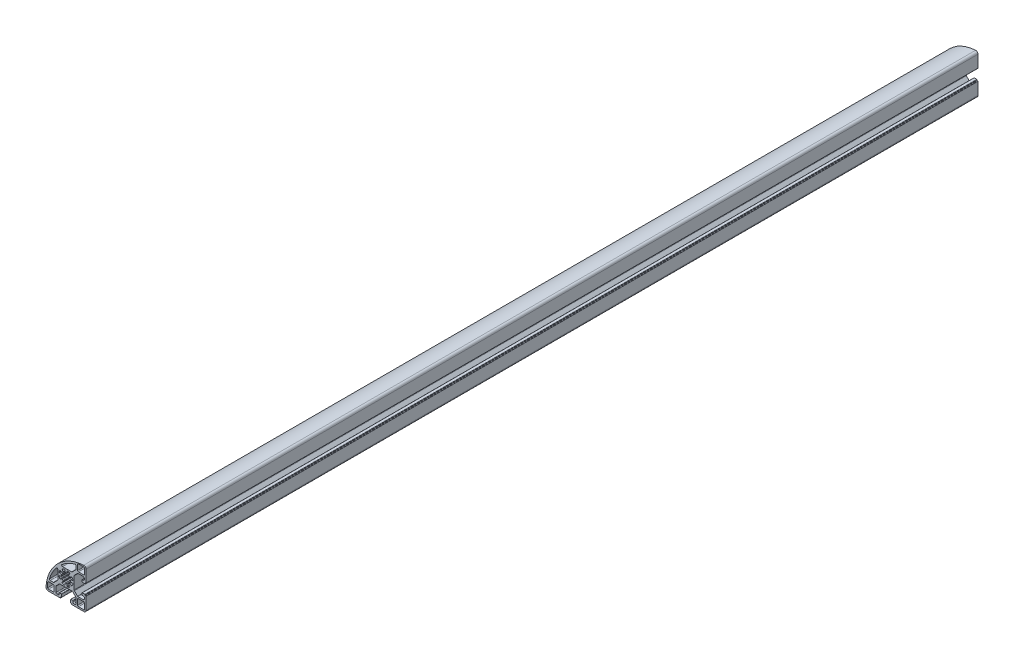
SolidWorks part; units mm, degrees
material "6063 T5"
ref_plane "Спереди" through (0, 0, 0) normal (0, 0, 1) x (1, 0, 0)
ref_plane "Сверху" through (0, 0, 0) normal (0, 1, 0) x (1, 0, 0)
ref_plane "Справа" through (0, 0, 0) normal (1, 0, 0) x (0, 0, -1)
sketch "Эскиз1" plane through (0, 0, 0) normal (0, 0, 1) x (1, 0, 0)
  line L0 (-19.98, 20.5457) -> (20.02, 20.5457) construction
  line L1 (11.25, -22.5) -> (20, -22.5)
  line L14 (22.5, -20) -> (22.5, -11.25)
  line L19 (-11.25, -22.5) -> (-19.9264, -22.5)
  line L20 (22.5, 19.9264) -> (22.5, 11.25)
  line L25 (0, 0) -> (22.5, -22.5) construction
  line L26 (-22.5383, 27.0237) -> (22.4617, 27.0237) construction
  line L27 (-22.4155, 26.5286) -> (22.5845, 26.5286) construction
  line L28 (14, -13) -> (19.8, -13)
  line L29 (13, -14) -> (13, -19.8)
  line L30 (14, -20.8) -> (19.8, -20.8)
  line L31 (20.8, -14) -> (20.8, -19.8)
  line L32 (-14.3, -13.3) -> (-19.5, -13.3)
  line L33 (-13.3, -14.3) -> (-13.3, -19.5)
  line L34 (-14.3, -20.5) -> (-19.5, -20.5)
  line L35 (-20.5, -14.3) -> (-20.5, -19.5)
  line L36 (14, 13) -> (19.8, 13)
  line L37 (13, 14) -> (13, 19.8)
  line L38 (14, 20.8) -> (19.8, 20.8)
  line L39 (20.8, 14) -> (20.8, 19.8)
  line L40 (-17.6738, -11.25) -> (-14.2165, -11.25)
  line L41 (-13.5094, -10.9571) -> (-9.4952, -6.9429)
  line L42 (-9.2023, -6.2358) -> (-9.2023, 3.8545)
  line L43 (10.9571, 13.5094) -> (6.9429, 9.4952)
  line L44 (11.25, 17.6738) -> (11.25, 14.2165)
  line L45 (6.2358, 9.2023) -> (-3.8545, 9.2023)
  arc A0 (-22.4221, -19.8529) -> (19.8529, 22.4221) centre (22.5, -22.5) cw
  arc A1 (13, -19.8) -> (14, -20.8) centre (14, -19.8) ccw
  arc A2 (19.8, -20.8) -> (20.8, -19.8) centre (19.8, -19.8) ccw
  arc A3 (19.8, -13) -> (20.8, -14) centre (19.8, -14) cw
  arc A4 (14, -13) -> (13, -14) centre (14, -14) ccw
  arc A5 (-19.5, -20.5) -> (-20.5, -19.5) centre (-19.5, -19.5) cw
  arc A6 (-13.3, -19.5) -> (-14.3, -20.5) centre (-14.3, -19.5) cw
  arc A7 (-14.3, -13.3) -> (-13.3, -14.3) centre (-14.3, -14.3) cw
  arc A8 (-19.5, -13.3) -> (-20.5, -14.3) centre (-19.5, -14.3) ccw
  arc A9 (19.8, 13) -> (20.8, 14) centre (19.8, 14) ccw
  arc A10 (14, 13) -> (13, 14) centre (14, 14) cw
  arc A11 (13, 19.8) -> (14, 20.8) centre (14, 19.8) cw
  arc A12 (19.8, 20.8) -> (20.8, 19.8) centre (19.8, 19.8) cw
  arc A14 (19.8529, 22.4221) -> (22.5, 19.9264) centre (20, 19.9264) cw
  arc A15 (20, -22.5) -> (22.5, -20) centre (20, -20) ccw
  arc A16 (-19.9264, -22.5) -> (-22.4221, -19.8529) centre (-19.9264, -20) cw
  arc A17 (-10.9809, 4.482) -> (-18.6304, -9.9583) centre (22.5, -22.5) ccw
  arc A18 (-9.4952, -6.9429) -> (-9.2023, -6.2358) centre (-10.2023, -6.2358) ccw
  arc A19 (-14.2165, -11.25) -> (-13.5094, -10.9571) centre (-14.2165, -10.25) ccw
  arc A20 (-17.6738, -11.25) -> (-18.6304, -9.9583) centre (-17.6738, -10.25) cw
  arc A21 (-9.2023, 3.8545) -> (-10.9809, 4.482) centre (-10.2023, 3.8545) ccw
  arc A22 (6.9429, 9.4952) -> (6.2358, 9.2023) centre (6.2358, 10.2023) cw
  arc A23 (11.25, 14.2165) -> (10.9571, 13.5094) centre (10.25, 14.2165) cw
  arc A24 (11.25, 17.6738) -> (9.9583, 18.6304) centre (10.25, 17.6738) ccw
  arc A25 (-4.482, 10.9809) -> (9.9583, 18.6304) centre (22.5, -22.5) cw
  arc A26 (-3.8545, 9.2023) -> (-4.482, 10.9809) centre (-3.8545, 10.2023) cw
  point P2 (0, 0)
  point P5 (0, 0)
  point P8 (0, 0)
  point P9 (0, 0)
  point P29 (20.8, -13)
  point P32 (13, -13)
  point P38 (-20.5, -20.5)
  point P41 (-13.3, -20.5)
  point P66 (-22.5, -22.5)
  point P74 (-9.2023, -6.65)
  point P77 (-13.8023, -11.25)
  point P80 (-19.0023, -11.25)
  line B0 (22.5, -11.25) -> (22.5, -6.4)
  line B1 (22.2, -6.1) -> (21.8, -6.1)
  line B2 (21.5, -5.8) -> (21.5, -5.4)
  line B3 (21.2, -5.1) -> (18.3, -5.1)
  line B4 (18, -5.4) -> (18, -7.3)
  line B5 (18.3, -7.6) -> (19.5, -7.6)
  line B6 (20.5, -8.6) -> (20.5, -10.25)
  line B7 (19.5, -11.25) -> (13.5642, -11.25)
  line B8 (12.8571, -10.9571) -> (9.4429, -7.5429)
  line B9 (9.15, -6.8358) -> (9.15, 6.8358)
  line B10 (9.15, 0) -> (22.5, 0) construction
  line B11 (12.8571, 10.9571) -> (9.4429, 7.5429)
  line B12 (19.5, 11.25) -> (13.5642, 11.25)
  line B13 (20.5, 8.6) -> (20.5, 10.25)
  line B14 (18.3, 7.6) -> (19.5, 7.6)
  line B15 (18, 5.4) -> (18, 7.3)
  line B16 (21.2, 5.1) -> (18.3, 5.1)
  line B17 (21.5, 5.8) -> (21.5, 5.4)
  line B18 (22.2, 6.1) -> (21.8, 6.1)
  line B19 (22.5, 11.25) -> (22.5, 6.4)
  arc B20 (18, -7.3) -> (18.3, -7.6) centre (18.3, -7.3) ccw
  arc B21 (18.3, -5.1) -> (18, -5.4) centre (18.3, -5.4) ccw
  arc B22 (21.5, -5.4) -> (21.2, -5.1) centre (21.2, -5.4) ccw
  arc B23 (21.8, -6.1) -> (21.5, -5.8) centre (21.8, -5.8) cw
  arc B24 (22.5, -6.4) -> (22.2, -6.1) centre (22.2, -6.4) ccw
  arc B25 (9.4429, -7.5429) -> (9.15, -6.8358) centre (10.15, -6.8358) cw
  arc B26 (13.5642, -11.25) -> (12.8571, -10.9571) centre (13.5642, -10.25) cw
  arc B27 (20.5, -10.25) -> (19.5, -11.25) centre (19.5, -10.25) cw
  arc B28 (19.5, -7.6) -> (20.5, -8.6) centre (19.5, -8.6) cw
  arc B29 (19.5, 7.6) -> (20.5, 8.6) centre (19.5, 8.6) ccw
  arc B30 (20.5, 10.25) -> (19.5, 11.25) centre (19.5, 10.25) ccw
  arc B31 (13.5642, 11.25) -> (12.8571, 10.9571) centre (13.5642, 10.25) ccw
  arc B32 (9.4429, 7.5429) -> (9.15, 6.8358) centre (10.15, 6.8358) ccw
  arc B33 (22.5, 6.4) -> (22.2, 6.1) centre (22.2, 6.4) cw
  arc B34 (21.8, 6.1) -> (21.5, 5.8) centre (21.8, 5.8) ccw
  arc B35 (21.5, 5.4) -> (21.2, 5.1) centre (21.2, 5.4) cw
  arc B36 (18.3, 5.1) -> (18, 5.4) centre (18.3, 5.4) cw
  arc B37 (18, 7.3) -> (18.3, 7.6) centre (18.3, 7.3) cw
  line B38 (0, 0) -> (3.6062, 3.6062) construction
  line B39 (1.3637, 7.358) -> (1.0164, 5.4842)
  line B40 (3.1592, 4.5967) -> (4.2386, 6.1672)
  line B41 (0, 0) -> (0, 5.1) construction
  arc B42 (0.478, -5.0776) -> (-0.478, -5.0776) centre (0, 0) cw
  arc B43 (-6.8804, -4.0816) -> (-7.7513, -1.979) centre (0, 0) cw
  arc B44 (3.9283, 3.2524) -> (3.2524, 3.9283) centre (0, 0) ccw
  arc B45 (4.0816, 6.8804) -> (1.979, 7.7513) centre (0, 0) ccw
  arc B46 (0.478, 5.0776) -> (-0.478, 5.0776) centre (0, 0) ccw
  line B47 (-1.3637, 7.358) -> (-1.0164, 5.4842)
  arc B48 (4.0816, -6.8804) -> (1.979, -7.7513) centre (0, 0) cw
  arc B49 (-3.9283, -3.2524) -> (-3.2524, -3.9283) centre (0, 0) ccw
  line B50 (-3.1592, -4.5967) -> (-4.2386, -6.1672)
  line B51 (0, 0) -> (6.3318, 0) construction
  line B52 (4.5967, 3.1592) -> (6.1672, 4.2386)
  line B53 (7.358, 1.3637) -> (5.4842, 1.0164)
  line B54 (-7.358, 1.3637) -> (-5.4842, 1.0164)
  line B55 (-4.5967, 3.1592) -> (-6.1672, 4.2386)
  line B56 (-3.1592, 4.5967) -> (-4.2386, 6.1672)
  line B57 (7.358, -1.3637) -> (5.4842, -1.0164)
  line B58 (4.5967, -3.1592) -> (6.1672, -4.2386)
  line B59 (3.1592, -4.5967) -> (4.2386, -6.1672)
  line B60 (1.3637, -7.358) -> (1.0164, -5.4842)
  line B61 (-1.3637, -7.358) -> (-1.0164, -5.4842)
  line B62 (-4.5967, -3.1592) -> (-6.1672, -4.2386)
  line B63 (-7.358, -1.3637) -> (-5.4842, -1.0164)
  arc B64 (5.0776, 0.478) -> (5.0776, -0.478) centre (0, 0) cw
  arc B65 (6.8804, 4.0816) -> (7.7513, 1.979) centre (0, 0) cw
  arc B66 (-5.0776, 0.478) -> (-5.0776, -0.478) centre (0, 0) ccw
  arc B67 (-6.8804, 4.0816) -> (-7.7513, 1.979) centre (0, 0) ccw
  arc B68 (-3.9283, 3.2524) -> (-3.2524, 3.9283) centre (0, 0) cw
  arc B69 (-4.0816, 6.8804) -> (-1.979, 7.7513) centre (0, 0) cw
  arc B70 (6.8804, -4.0816) -> (7.7513, -1.979) centre (0, 0) ccw
  arc B71 (3.9283, -3.2524) -> (3.2524, -3.9283) centre (0, 0) cw
  arc B72 (-4.0816, -6.8804) -> (-1.979, -7.7513) centre (0, 0) ccw
  arc B73 (5.0776, 0.478) -> (5.4842, 1.0164) centre (5.5754, 0.5248) cw
  arc B74 (5.4842, -1.0164) -> (5.0776, -0.478) centre (5.5754, -0.5248) cw
  arc B75 (7.7513, -1.979) -> (7.358, -1.3637) centre (7.2669, -1.8554) ccw
  arc B76 (6.8804, -4.0816) -> (6.1672, -4.2386) centre (6.4504, -3.8265) cw
  arc B77 (3.9283, -3.2524) -> (4.5967, -3.1592) centre (4.3135, -3.5713) cw
  arc B78 (3.2524, -3.9283) -> (3.1592, -4.5967) centre (3.5713, -4.3135) ccw
  arc B79 (4.0816, -6.8804) -> (4.2386, -6.1672) centre (3.8265, -6.4504) ccw
  arc B80 (1.979, -7.7513) -> (1.3637, -7.358) centre (1.8554, -7.2669) cw
  arc B81 (0.478, -5.0776) -> (1.0164, -5.4842) centre (0.5248, -5.5754) cw
  arc B82 (-0.478, -5.0776) -> (-1.0164, -5.4842) centre (-0.5248, -5.5754) ccw
  arc B83 (-1.979, -7.7513) -> (-1.3637, -7.358) centre (-1.8554, -7.2669) ccw
  arc B84 (-4.0816, -6.8804) -> (-4.2386, -6.1672) centre (-3.8265, -6.4504) cw
  arc B85 (-3.2524, -3.9283) -> (-3.1592, -4.5967) centre (-3.5713, -4.3135) cw
  arc B86 (-3.9283, -3.2524) -> (-4.5967, -3.1592) centre (-4.3135, -3.5713) ccw
  arc B87 (-6.8804, -4.0816) -> (-6.1672, -4.2386) centre (-6.4504, -3.8265) ccw
  arc B88 (-7.7513, -1.979) -> (-7.358, -1.3637) centre (-7.2669, -1.8554) cw
  arc B89 (-5.4842, -1.0164) -> (-5.0776, -0.478) centre (-5.5754, -0.5248) ccw
  arc B90 (-5.0776, 0.478) -> (-5.4842, 1.0164) centre (-5.5754, 0.5248) ccw
  arc B91 (-7.7513, 1.979) -> (-7.358, 1.3637) centre (-7.2669, 1.8554) ccw
  arc B92 (-6.8804, 4.0816) -> (-6.1672, 4.2386) centre (-6.4504, 3.8265) cw
  arc B93 (-3.9283, 3.2524) -> (-4.5967, 3.1592) centre (-4.3135, 3.5713) cw
  arc B94 (-3.2524, 3.9283) -> (-3.1592, 4.5967) centre (-3.5713, 4.3135) ccw
  arc B95 (-4.0816, 6.8804) -> (-4.2386, 6.1672) centre (-3.8265, 6.4504) ccw
  arc B96 (-1.979, 7.7513) -> (-1.3637, 7.358) centre (-1.8554, 7.2669) cw
  arc B97 (-1.0164, 5.4842) -> (-0.478, 5.0776) centre (-0.5248, 5.5754) ccw
  arc B98 (1.0164, 5.4842) -> (0.478, 5.0776) centre (0.5248, 5.5754) cw
  arc B99 (1.3637, 7.358) -> (1.979, 7.7513) centre (1.8554, 7.2669) cw
  arc B100 (4.2386, 6.1672) -> (4.0816, 6.8804) centre (3.8265, 6.4504) ccw
  arc B101 (3.1592, 4.5967) -> (3.2524, 3.9283) centre (3.5713, 4.3135) ccw
  arc B102 (4.5967, 3.1592) -> (3.9283, 3.2524) centre (4.3135, 3.5713) cw
  arc B103 (6.1672, 4.2386) -> (6.8804, 4.0816) centre (6.4504, 3.8265) cw
  arc B104 (7.7513, 1.979) -> (7.358, 1.3637) centre (7.2669, 1.8554) cw
  line B105 (-11.25, -22.5) -> (-6.4, -22.5)
  line B106 (-6.1, -22.2) -> (-6.1, -21.8)
  line B107 (-5.8, -21.5) -> (-5.4, -21.5)
  line B108 (-5.1, -21.2) -> (-5.1, -18.3)
  line B109 (-5.4, -18) -> (-7.3, -18)
  line B110 (-7.6, -18.3) -> (-7.6, -19.5)
  line B111 (-8.6, -20.5) -> (-10.25, -20.5)
  line B112 (-11.25, -19.5) -> (-11.25, -13.5642)
  line B113 (-10.9571, -12.8571) -> (-7.5429, -9.4429)
  line B114 (-6.8358, -9.15) -> (6.8358, -9.15)
  line B115 (0, -9.15) -> (0, -22.5) construction
  line B116 (10.9571, -12.8571) -> (7.5429, -9.4429)
  line B117 (11.25, -19.5) -> (11.25, -13.5642)
  line B118 (8.6, -20.5) -> (10.25, -20.5)
  line B119 (7.6, -18.3) -> (7.6, -19.5)
  line B120 (5.4, -18) -> (7.3, -18)
  line B121 (5.1, -21.2) -> (5.1, -18.3)
  line B122 (5.8, -21.5) -> (5.4, -21.5)
  line B123 (6.1, -22.2) -> (6.1, -21.8)
  line B124 (11.25, -22.5) -> (6.4, -22.5)
  arc B125 (-7.3, -18) -> (-7.6, -18.3) centre (-7.3, -18.3) ccw
  arc B126 (-5.1, -18.3) -> (-5.4, -18) centre (-5.4, -18.3) ccw
  arc B127 (-5.4, -21.5) -> (-5.1, -21.2) centre (-5.4, -21.2) ccw
  arc B128 (-6.1, -21.8) -> (-5.8, -21.5) centre (-5.8, -21.8) cw
  arc B129 (-6.4, -22.5) -> (-6.1, -22.2) centre (-6.4, -22.2) ccw
  arc B130 (-7.5429, -9.4429) -> (-6.8358, -9.15) centre (-6.8358, -10.15) cw
  arc B131 (-11.25, -13.5642) -> (-10.9571, -12.8571) centre (-10.25, -13.5642) cw
  arc B132 (-10.25, -20.5) -> (-11.25, -19.5) centre (-10.25, -19.5) cw
  arc B133 (-7.6, -19.5) -> (-8.6, -20.5) centre (-8.6, -19.5) cw
  arc B134 (7.6, -19.5) -> (8.6, -20.5) centre (8.6, -19.5) ccw
  arc B135 (10.25, -20.5) -> (11.25, -19.5) centre (10.25, -19.5) ccw
  arc B136 (11.25, -13.5642) -> (10.9571, -12.8571) centre (10.25, -13.5642) ccw
  arc B137 (7.5429, -9.4429) -> (6.8358, -9.15) centre (6.8358, -10.15) ccw
  arc B138 (6.4, -22.5) -> (6.1, -22.2) centre (6.4, -22.2) cw
  arc B139 (6.1, -21.8) -> (5.8, -21.5) centre (5.8, -21.8) ccw
  arc B140 (5.4, -21.5) -> (5.1, -21.2) centre (5.4, -21.2) cw
  arc B141 (5.1, -18.3) -> (5.4, -18) centre (5.4, -18.3) cw
  arc B142 (7.3, -18) -> (7.6, -18.3) centre (7.3, -18.3) cw
  dimension "D12" = 2
  dimension "D13" = 1
  dimension "D2" = 22.5
  dimension "D3" = 45
  dimension "D5" = 1.7
  dimension "D6" = 1.7
  dimension "D4" = 45
  dimension "D9" = 1
  dimension "D14" = 2.5
  dimension "D15" = 43
  dimension "D19" = 1
  dimension "D1" = 22.5
  dimension "D7" = 45
  dimension "D8" = 7.8
  dimension "D10" = 2
  dimension "D11" = 7.2
  dimension "D16" = 135
  dimension "D17" = 5.2
  dimension "D18" = 4.6
sketch_block_instance "8B(20,5PL)-4"
sketch_block "8B(20,5PL)" parameters "D7"=0.3, "D8"=1, "D1"=13.35, "D2"=4.5, "D3"=10.2, "D4"=22.5, "D5"=12.2, "D6"=135, "D9"=11.8, "D10"=4.85, "D11"=1.4, "D12"=1.65
sketch_block_instance "star_R5,1_R8-1"
sketch_block "star_R5,1_R8" parameters "D1"=10.2, "D5"=16, "D6"=0.5, "D2"=10.5, "D3"=24, "D4"=45
sketch_block_instance "8B(20,5PL)-9"
extrude "Бобышка-Вытянуть1" add sketch "Эскиз1" along normal blind 1000 contours B142 B120 B141 B121 B140 B122 B139 B123 B138 B124 L1 A15 L14 B0 B24 B1 B23 B2 B22 B3 B21 B4 B20 B5 B28 B6 B27 B7 B26 B8 B25 B9 B32 B11 B31 B12 B30 B13 B29 B14 B37 B15 B36 B16 B35 B17 B34 B18 B33 B19 L20
